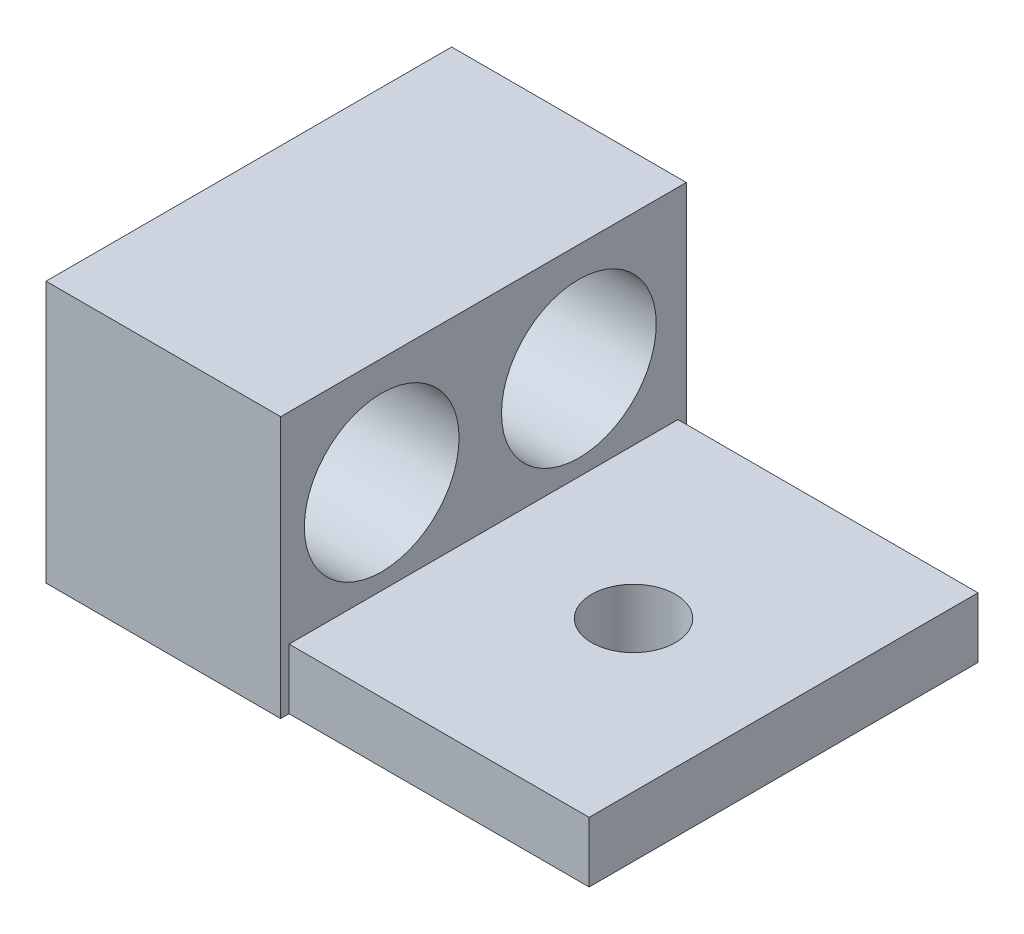
SolidWorks part; units mm, degrees
ref_plane "Front Plane" through (0, 0, 0) normal (0, 0, 1) x (1, 0, 0)
ref_plane "Top Plane" through (0, 0, 0) normal (0, 1, 0) x (1, 0, 0)
ref_plane "Right Plane" through (0, 0, 0) normal (1, 0, 0) x (0, 0, -1)
sketch "Sketch1" plane through (0, 0, 0) normal (0, 0, 1) x (1, 0, 0)
  line L1 (0, 0) -> (81.026, 0)
  line L2 (0, 0) -> (0, 39.624)
  line L3 (0, 39.624) -> (81.026, 39.624)
  line L4 (81.026, 0) -> (81.026, 39.624)
  dimension "D1" = 81.026
  dimension "D2" = 39.624
extrude "Boss-Extrude1" add sketch "Sketch1" against normal blind 61.468
sketch "Sketch5" plane through (0, 0, 0) normal (0, 0, 1) x (1, 0, 0)
  line L1 (81.026, 39.624) -> (35.56, 39.624)
  line L2 (81.026, 39.624) -> (81.026, 9.144)
  line L3 (81.026, 9.144) -> (35.56, 9.144)
  line L4 (35.56, 39.624) -> (35.56, 9.144)
  dimension "D1" = 30.48
  dimension "D2" = 45.466
extrude "Cut-Extrude1" cut sketch "Sketch5" against normal through all
sketch "Sketch6" plane through (0, 9.144, 0) normal (0, 1, 0) x (1, 0, 0)
  line L0 (35.56, 61.468) -> (35.56, 0) construction
  line L1 (81.026, 0) -> (35.56, 0)
  line L2 (81.026, 0) -> (81.026, 1.27)
  line L3 (81.026, 1.27) -> (35.56, 1.27)
  line L4 (35.56, 0) -> (35.56, 1.27)
  line L6 (81.026, 61.468) -> (35.56, 61.468)
  line L7 (81.026, 61.468) -> (81.026, 60.198)
  line L8 (81.026, 60.198) -> (35.56, 60.198)
  line L9 (35.56, 61.468) -> (35.56, 60.198)
  dimension "D1" = 1.27
  dimension "D2" = 1.27
extrude "Cut-Extrude2" cut sketch "Sketch6" against normal through all
sketch "Sketch7" plane through (0, 9.144, 0) normal (0, 1, 0) x (1, 0, 0)
  line L0 (81.026, 30.734) -> (35.56, 30.734) construction
  line L1 (81.026, 60.198) -> (81.026, 1.27) construction
  line L2 (35.56, 60.198) -> (35.56, 1.27) construction
  line L3 (58.293, 1.27) -> (58.293, 60.198) construction
  line L4 (81.026, 1.27) -> (35.56, 1.27) construction
  line L5 (35.56, 60.198) -> (81.026, 60.198) construction
  circle A0 centre (58.293, 30.734) radius 6.35
  point P8 (58.293, 30.734)
  point P15 (58.293, 30.734)
extrude "Cut-Extrude3" cut sketch "Sketch7" against normal through all
sketch "Sketch8" plane through (35.56, 0, 0) normal (1, 0, 0) x (0, 0, -1)
  line L0 (0, 23.3372) -> (61.468, 23.3372) construction
  line L1 (0, 39.624) -> (0, 0) construction
  line L2 (61.468, 39.624) -> (61.468, 0) construction
  circle A0 centre (15.3073, 23.3372) radius 11.7221
  circle A1 centre (45.1845, 23.3372) radius 11.7221
extrude "Cut-Extrude4" cut sketch "Sketch8" against normal through all
